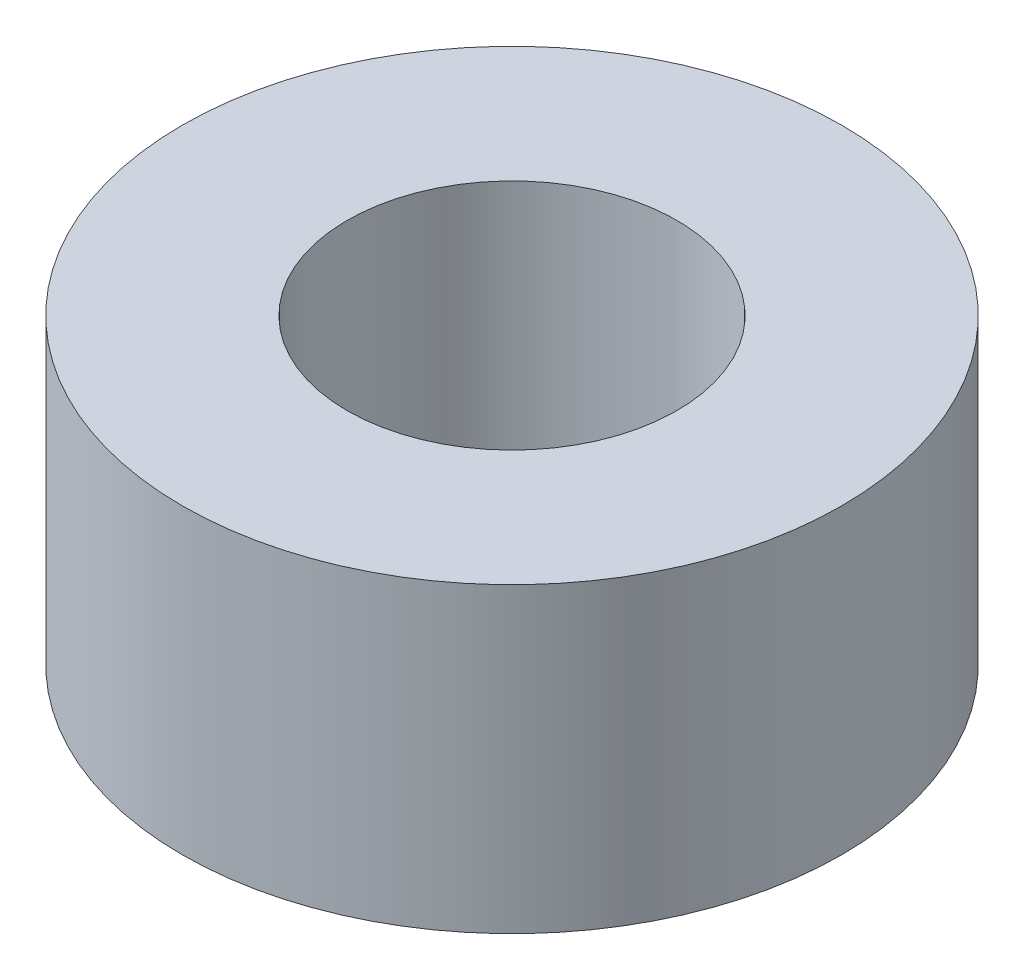
SolidWorks part; units mm, degrees
ref_plane "정면" through (0, 0, 0) normal (0, 0, 1) x (1, 0, 0)
ref_plane "윗면" through (0, 0, 0) normal (0, 1, 0) x (1, 0, 0)
ref_plane "우측면" through (0, 0, 0) normal (1, 0, 0) x (0, 0, -1)
sketch "스케치1" plane through (0, 0, 0) normal (0, 1, 0) x (1, 0, 0)
  circle A0 centre (0, 0) radius 6
  circle A1 centre (0, 0) radius 3
  dimension "D1" = 12
  dimension "D2" = 6
extrude "보스-돌출1" add sketch "스케치1" along normal blind 5.5 contours A0 | A1
